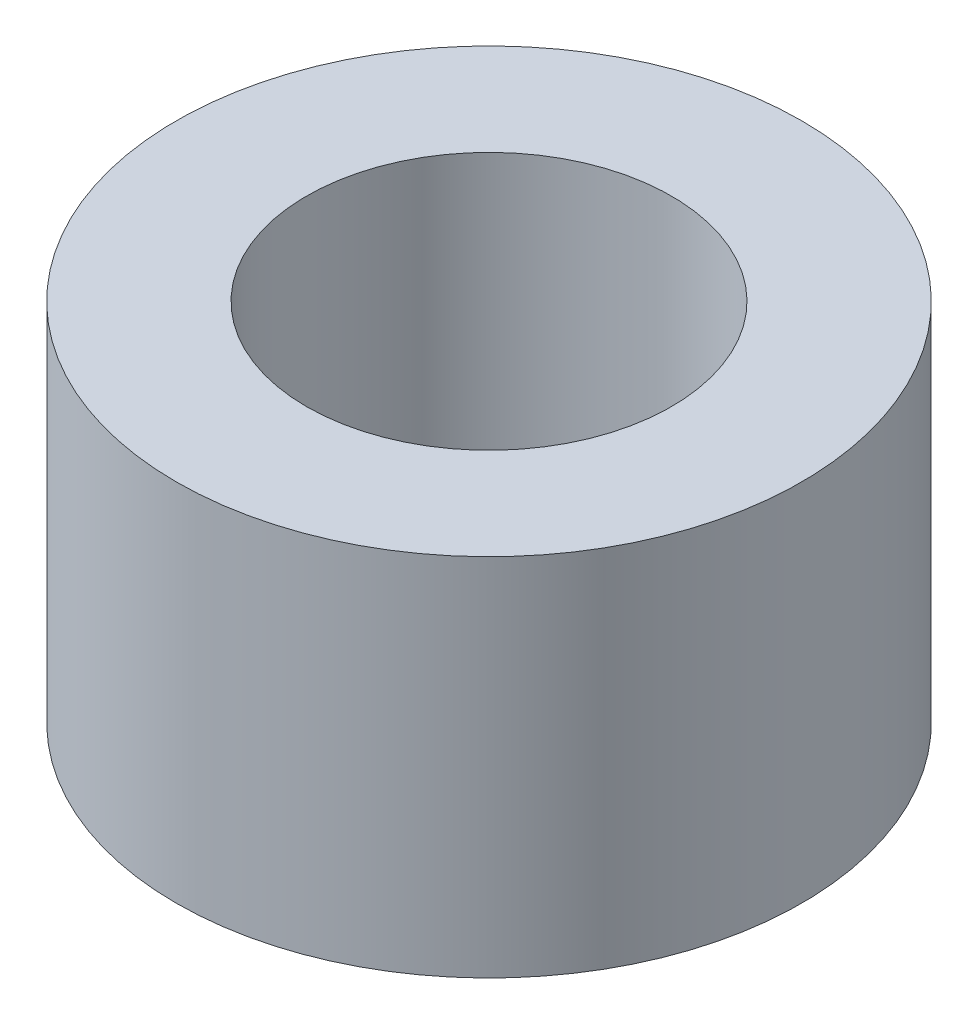
SolidWorks part; units mm, degrees
ref_plane "Plan de face" through (0, 0, 0) normal (0, 0, 1) x (1, 0, 0)
ref_plane "Plan de dessus" through (0, 0, 0) normal (0, 1, 0) x (1, 0, 0)
ref_plane "Plan de droite" through (0, 0, 0) normal (1, 0, 0) x (0, 0, -1)
sketch "Esquisse1" plane through (0, 0, 0) normal (1, 0, 0) x (0, 0, -1)
  line L0 (0, 3.7796) -> (0, -5.8299) construction
  line L2 (1.75, 3.5) -> (3, 3.5)
  line L3 (1.75, 3.5) -> (1.75, 0)
  line L4 (1.75, 0) -> (3, 0)
  line L5 (3, 3.5) -> (3, 0)
  dimension "D1" = 6
  dimension "D2" = 3.5
  dimension "D3" = 3.5
revolve "Révolution1" add sketch "Esquisse1" angle 360 about L0
